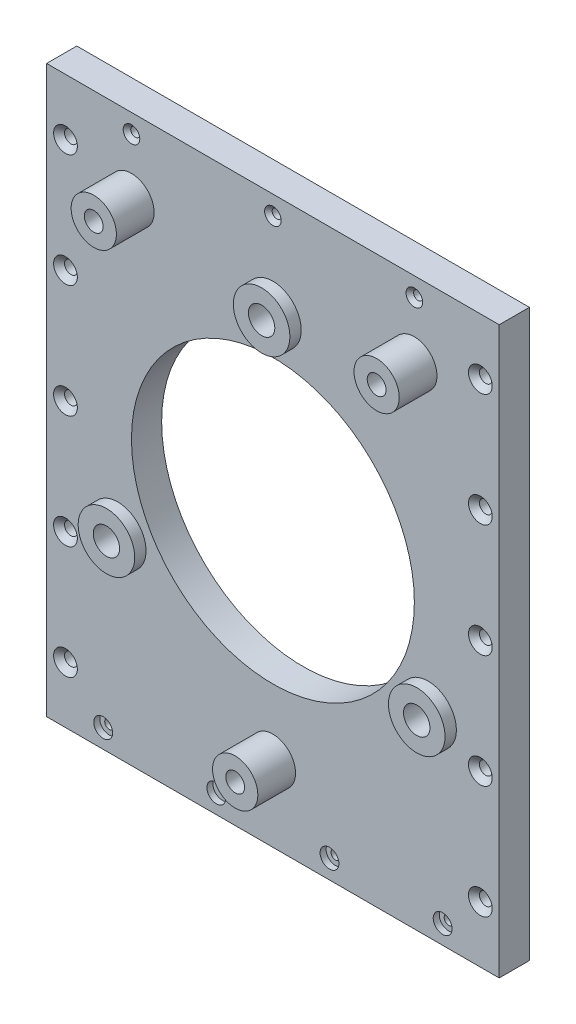
SolidWorks part; units mm, degrees
ref_plane "Front Plane" through (0, 0, 0) normal (0, 0, 1) x (1, 0, 0)
ref_plane "Top Plane" through (0, 0, 0) normal (0, 1, 0) x (1, 0, 0)
ref_plane "Right Plane" through (0, 0, 0) normal (1, 0, 0) x (0, 0, -1)
other "Configuration Table"
sketch "Sketch1" plane through (0, 0, 0) normal (0, 0, 1) x (1, 0, 0)
  line L1 (0, 0) -> (120, 0)
  line L2 (0, 0) -> (0, 150)
  line L3 (0, 150) -> (120, 150)
  line L4 (120, 0) -> (120, 150)
  dimension "D1" = 150
  dimension "D2" = 120
extrude "Extrude1" add sketch "Sketch1" against normal blind 8
sketch "Sketch2" plane through (0, 0, 0) normal (0, 0, 1) x (1, 0, 0)
  line L0 (0, 0) -> (120, 150) construction
  circle A0 centre (60, 75) radius 37.5
  point P3 (60, 75)
  dimension "D1" = 75
extrude "Extrude2" cut sketch "Sketch2" against normal through all
sketch "Sketch3" plane through (0, 0, 0) normal (0, 0, 1) x (1, 0, 0)
  line L0 (60, 75) -> (60, 122.5) construction
  circle A0 centre (60, 122.5) radius 7.5
  circle A1 centre (101.1362, 51.25) radius 7.5
  circle A2 centre (18.8638, 51.25) radius 7.5
  dimension "D1" = 15
  dimension "D2" = 47.5
extrude "Extrude3" add sketch "Sketch3" along normal blind 3
sketch "Sketch4" plane through (0, 0, 0) normal (0, 0, 1) x (1, 0, 0)
  circle A0 centre (22.5, 130) radius 6
  circle A1 centre (97.5, 130) radius 6
  circle A2 centre (60, 20) radius 6
  point P2 (60, 75)
  dimension "D4" = 12
  dimension "D1" = 37.5
  dimension "D2" = 55
  dimension "D3" = 55
extrude "Extrude4" add sketch "Sketch4" along normal blind 10
hole_wizard " Tapped Hole1" positions "Sketch6" profile "Sketch5" tap size "M5x0.8" standard "Ansi Metric"
sketch "Sketch6" plane through (0, 0, 10) normal (0, 0, 1) x (1, 0, 0)
  circle A0 centre (22.5, 130) radius 6 construction
  point P0 (22.5, 130)
  point P1 (97.5, 130)
  point P4 (60, 20)
sketch "Sketch5" plane through (22.5, 130, 10) normal (1, 0, 0) x (0, -1, 0)
  line L0 (0, 0) -> (0, 15.2618)
  line L1 (0, 15.2618) -> (2.1, 14)
  line L2 (2.1, 14) -> (2.1, 10)
  line L3 (2.1, 10) -> (2.5, 10)
  line L4 (2.5, 10) -> (2.5, 0)
  line L5 (2.5, 0) -> (0, 0)
  line L10 (0, 15.2618) -> (-2.1, 14) construction
  line L11 (0, -6.35) -> (0, 107.95) construction
  dimension "Tap Drill Dia." = 4.2
  dimension "Tap Drill Depth" = 14
  dimension "Thread Major Dia." = 5
  dimension "Thread Depth" = 10
  dimension "Drill Angle" = 118
sketch "Sketch7" plane through (0, 0, 3) normal (0, 0, 1) x (1, 0, 0)
  circle A0 centre (60, 122.5) radius 3.5
  circle A1 centre (101.1362, 51.25) radius 3.5
  circle A2 centre (18.8638, 51.25) radius 3.5
  dimension "D1" = 7
extrude "Extrude5" cut sketch "Sketch7" against normal through all
hole_wizard "CSK for  Flat Head Machine Screw1" positions "Sketch9" profile "Sketch8" countersink size "M3" standard "Ansi Metric" end condition through all
sketch "Sketch9" plane through (0, 0, 0) normal (0, 0, 1) x (1, 0, 0)
  line L0 (0, 150) -> (0, 0) construction
  line L1 (0, 0) -> (120, 0) construction
  point P0 (5, 15)
  dimension "D1" = 5
  dimension "D2" = 15
sketch "Sketch8" plane through (5, 15, 0) normal (1, 0, 0) x (0, -1, 0)
  line L0 (0, 0) -> (0, 8)
  line L1 (0, 8) -> (1.7, 8)
  line L2 (1.7, 8) -> (1.7, 1.45)
  line L3 (1.7, 1.45) -> (3.15, 0)
  line L5 (3.15, 0) -> (0, 0)
  line L6 (-1.7, 1.45) -> (-3.15, 0) construction
  line L11 (0, -6.35) -> (0, 107.95) construction
  dimension "Thru Hole Dia." = 3.4
  dimension "Thru Hole Depth" = 8
  dimension "Near C'Sink Dia." = 6.3
  dimension "Near C'Sink Angle" = 90
pattern_linear "LPattern1" count 5 spacing 30 along (0, 1, 0) count 2 spacing 110 along (1, 0, 0) of "CSK for  Flat Head Machine Screw1"
hole_wizard "CBORE for  Pan Head Machine Screw2" positions "Sketch11" profile "Sketch10" counterbore size "M2" standard "Ansi Metric" end condition through all
sketch "Sketch11" plane through (0, 0, 0) normal (0, 0, 1) x (1, 0, 0)
  line L0 (0, 0) -> (120, 0) construction
  line L1 (0, 150) -> (0, 0) construction
  point P0 (15, 5)
  dimension "D1" = 5
  dimension "D2" = 15
sketch "Sketch10" plane through (15, 5, 0) normal (1, 0, 0) x (0, -1, 0)
  line L0 (0, 0) -> (0, 8)
  line L1 (0, 8) -> (1.2, 8)
  line L3 (1.2, 8) -> (1.2, 1.6)
  line L4 (1.2, 1.6) -> (2.5, 1.6)
  line L5 (2.5, 1.6) -> (2.5, 0)
  line L7 (2.5, 0) -> (0, 0)
  line L11 (0, -6.35) -> (0, 107.95) construction
  dimension "Thru Hole Dia." = 2.4
  dimension "Thru Hole Depth" = 8
  dimension "C'Bore Dia." = 5
  dimension "C'Bore Depth" = 1.6
pattern_linear "LPattern2" count 4 spacing 30 along (1, 0, 0) of "CBORE for  Pan Head Machine Screw2"
hole_wizard "CSK for  Flat Head Machine Screw2" positions "Sketch13" profile "Sketch12" countersink size "M2" standard "Ansi Metric" end condition through all
sketch "Sketch13" plane through (0, 0, 0) normal (0, 0, 1) x (1, 0, 0)
  line L0 (120, 150) -> (0, 150) construction
  circle A0 centre (60, 75) radius 37.5 construction
  point P0 (22.5, 145)
  dimension "D1" = 37.5
  dimension "D2" = 5
sketch "Sketch12" plane through (22.5, 145, 0) normal (1, 0, 0) x (0, -1, 0)
  line L0 (0, 0) -> (0, 8)
  line L1 (0, 8) -> (1.2, 8)
  line L2 (1.2, 8) -> (1.2, 1)
  line L3 (1.2, 1) -> (2.2, 0)
  line L5 (2.2, 0) -> (0, 0)
  line L6 (-1.2, 1) -> (-2.2, 0) construction
  line L11 (0, -6.35) -> (0, 107.95) construction
  dimension "Thru Hole Dia." = 2.4
  dimension "Thru Hole Depth" = 8
  dimension "Near C'Sink Dia." = 4.4
  dimension "Near C'Sink Angle" = 90
pattern_linear "LPattern3" count 3 spacing 37.5 along (1, 0, 0) of "CSK for  Flat Head Machine Screw2"
